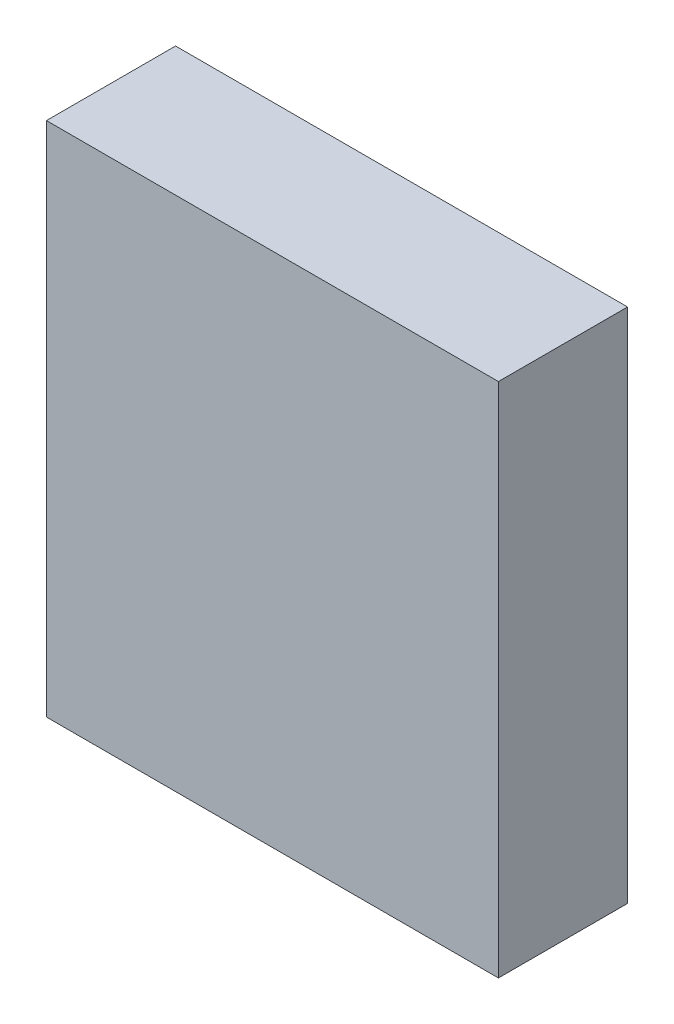
SolidWorks part; units mm, degrees
ref_plane "Front Plane" through (0, 0, 0) normal (0, 0, 1) x (1, 0, 0)
ref_plane "Top Plane" through (0, 0, 0) normal (0, 1, 0) x (1, 0, 0)
ref_plane "Right Plane" through (0, 0, 0) normal (1, 0, 0) x (0, 0, -1)
sketch "Sketch1" plane through (0, 0, 0) normal (0, 1, 0) x (1, 0, 0)
  line L1 (0, 0) -> (35, 0)
  line L2 (0, 0) -> (0, 10)
  line L3 (0, 10) -> (35, 10)
  line L4 (35, 0) -> (35, 10)
extrude "Boss-Extrude1" add sketch "Sketch1" along normal blind 40
